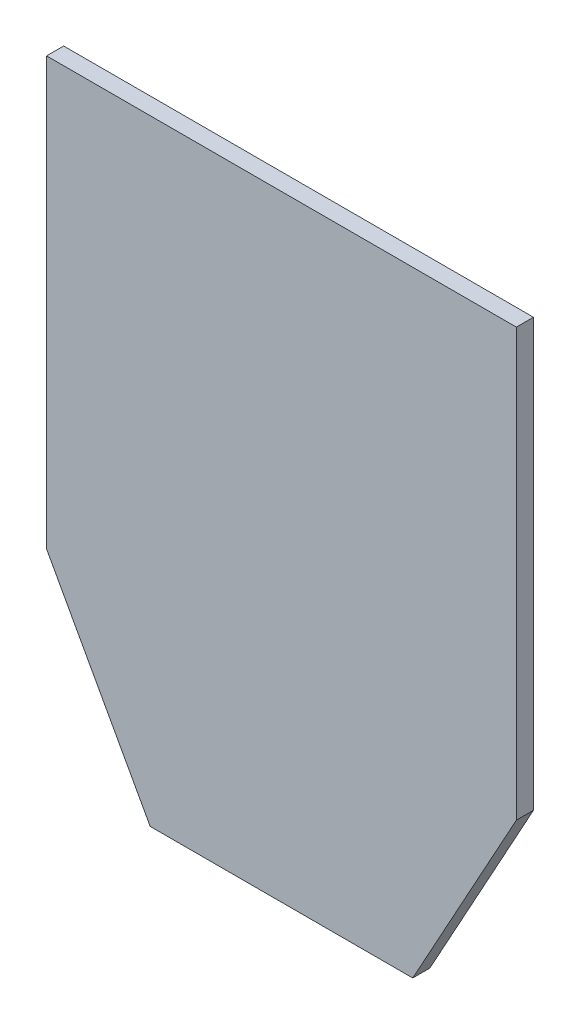
SolidWorks part; units mm, degrees
ref_plane "Front Plane" through (0, 0, 0) normal (0, 0, 1) x (1, 0, 0)
ref_plane "Top Plane" through (0, 0, 0) normal (0, 1, 0) x (1, 0, 0)
ref_plane "Right Plane" through (0, 0, 0) normal (1, 0, 0) x (0, 0, -1)
sketch "Sketch1" plane through (0, 0, 0) normal (0, 0, 1) x (1, 0, 0)
  line L0 (-38.5086, 29.1176) -> (71.4914, 29.1176)
  line L1 (-38.5086, 29.1176) -> (-38.5086, -70.8824)
  line L2 (71.4914, 29.1176) -> (71.4914, -70.8824)
  line L11 (-14.2483, -115.008) -> (47.231, -115.008)
  line L15 (-38.5086, -70.8824) -> (-14.2483, -115.008)
  line L16 (47.231, -115.008) -> (71.4914, -70.8824)
  point P2 (-38.5086, 29.1176)
  point P9 (16.4914, -115.008)
extrude "Boss-Extrude1" add sketch "Sketch1" along normal blind 4
